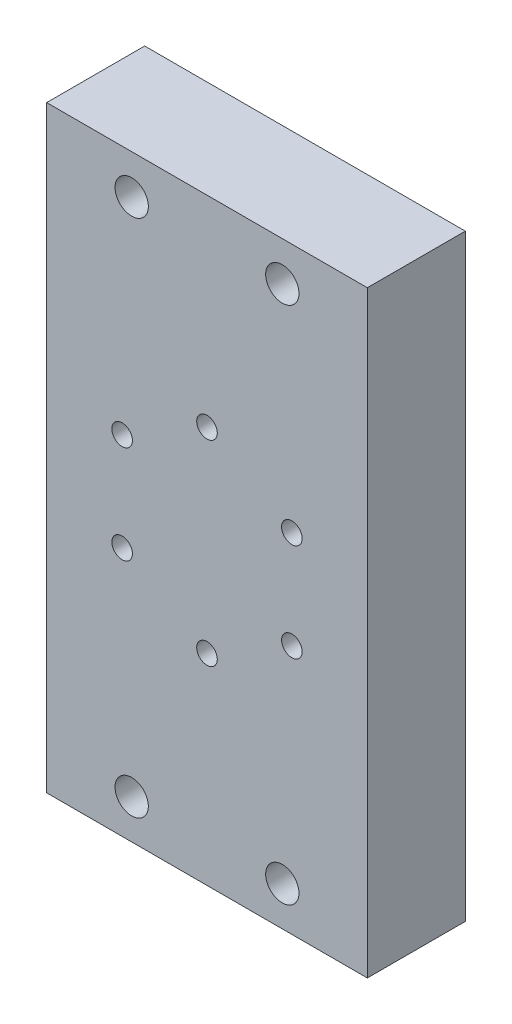
SolidWorks part; units mm, degrees
ref_plane "Front Plane" through (0, 0, 0) normal (0, 0, 1) x (1, 0, 0)
ref_plane "Top Plane" through (0, 0, 0) normal (0, 1, 0) x (1, 0, 0)
ref_plane "Right Plane" through (0, 0, 0) normal (1, 0, 0) x (0, 0, -1)
sketch "Sketch1" plane through (0, 0, 0) normal (0, 0, 1) x (1, 0, 0)
  line L1 (-32.72, -61) -> (32.72, -61)
  line L2 (-32.72, -61) -> (-32.72, 61)
  line L3 (-32.72, 61) -> (32.72, 61)
  line L4 (32.72, -61) -> (32.72, 61)
  line L5 (-32.72, -61) -> (32.72, 61) construction
  line L6 (-32.72, 61) -> (32.72, -61) construction
  point P0 (0, 0)
  dimension "D1" = 122
  dimension "D2" = 65.44
extrude "Boss-Extrude1" add sketch "Sketch1" along normal blind 20
sketch "Sketch2" plane through (0, 0, 20) normal (0, 0, 1) x (1, 0, 0)
  line L0 (0, 0) -> (32.72, 0) construction
  line L1 (32.72, -61) -> (32.72, 61) construction
  line L2 (0, 0) -> (0, 61) construction
  line L3 (32.72, 61) -> (-32.72, 61) construction
  circle A0 centre (0, 0) radius 20
  point P3 (0, 20)
  point P4 (17.3205, 10)
  point P7 (17.3205, -10)
  point P8 (0, -20)
  point P9 (-17.3205, -10)
  point P10 (-17.3205, 10)
  point P15 (-15.37, 53)
  point P16 (0, 0)
  point P17 (15.37, 53)
  point P18 (15.37, -53)
  point P19 (-15.37, -53)
  dimension "D1" = 40
  dimension "D3" = 8
  dimension "D4" = 15.37
  dimension "D2" = 6
hole_wizard "M5x0.8 Tapped Hole1" positions "Sketch10" profile "Sketch11" tap size "M5x0.8" standard "ANSI Metric" end condition up to next
sketch "Sketch10" plane through (0, 0, 20) normal (0, 0, 1) x (1, 0, 0)
  point P0 (0, 20)
  point P3 (-17.3205, 10)
  point P6 (-17.3205, -10)
  point P9 (0, -20)
  point P12 (17.3205, -10)
  point P15 (17.3205, 10)
sketch "Sketch11" plane through (0, 20, 20) normal (1, 0, 0) x (0, -1, 0)
  line L0 (0, 0) -> (0, 20)
  line L1 (0, 20) -> (2.1, 20)
  line L2 (2.1, 20) -> (2.1, 0)
  line L5 (2.1, 0) -> (0, 0)
  line L11 (0, -6.35) -> (0, 107.95) construction
  dimension "Thread Major Dia." = 4.2
  dimension "Thru Tap Drill Depth" = 20
hole_wizard "M8x1.25 Tapped Hole1" positions "Sketch12" profile "Sketch13" tap size "M8x1.25" standard "ANSI Metric" end condition up to next
sketch "Sketch12" plane through (0, 0, 20) normal (0, 0, 1) x (1, 0, 0)
  point P0 (-15.37, 53)
  point P3 (15.37, 53)
  point P6 (15.37, -53)
  point P9 (-15.37, -53)
sketch "Sketch13" plane through (-15.37, 53, 20) normal (1, 0, 0) x (0, -1, 0)
  line L0 (0, 0) -> (0, 20)
  line L1 (0, 20) -> (3.4, 20)
  line L2 (3.4, 20) -> (3.4, 0)
  line L5 (3.4, 0) -> (0, 0)
  line L11 (0, -6.35) -> (0, 107.95) construction
  dimension "Thread Major Dia." = 6.8
  dimension "Thru Tap Drill Depth" = 20
